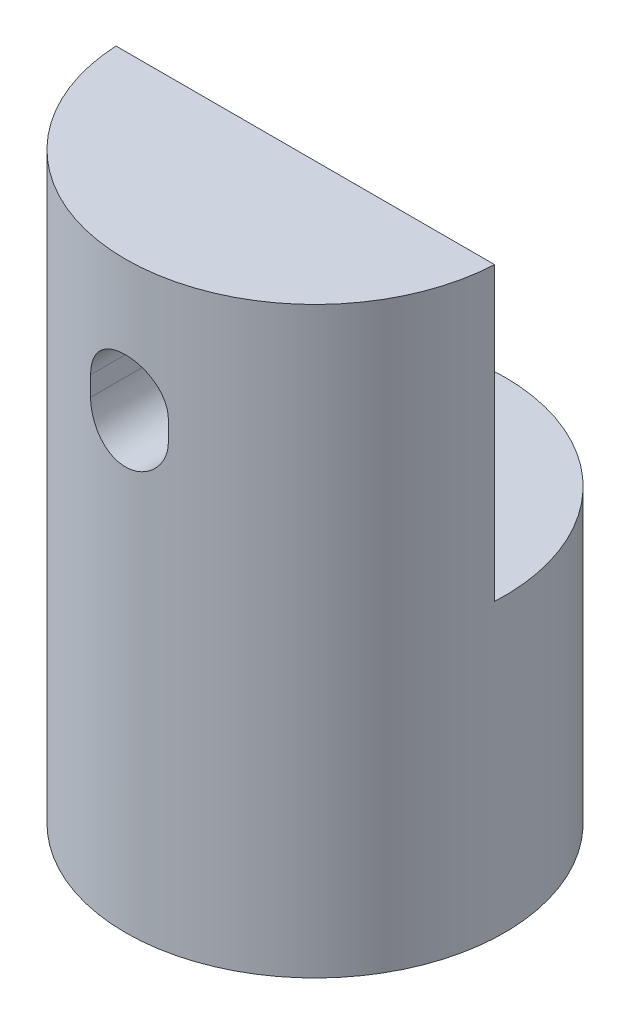
SolidWorks part; units mm, degrees
material "20% infill ABS"
ref_plane "Front" through (0, 0, 0) normal (0, 0, 1) x (1, 0, 0)
ref_plane "Top" through (0, 0, 0) normal (0, 1, 0) x (1, 0, 0)
ref_plane "Right" through (0, 0, 0) normal (1, 0, 0) x (0, 0, -1)
sketch "Sketch1" plane through (0, 0, 0) normal (0, 1, 0) x (1, 0, 0)
  circle A0 centre (0, 0) radius 9.75
  dimension "D1" = 19.5
extrude "Boss-Extrude1" add sketch "Sketch1" along normal blind 30
ref_plane "Plane1" through (9.75, 0, 0) normal (1, 0, 0) x (0, 0, -1)
sketch "Sketch3" plane through (0, 0, 0) normal (0, 0, 1) x (1, 0, 0)
  line L0 (9.75, -10.725) -> (9.75, 10.725) construction
  line L1 (-9.75, 30) -> (9.75, 30)
  line L2 (-9.75, 30) -> (-9.75, 15)
  line L3 (-9.75, 15) -> (9.75, 15)
  line L4 (9.75, 30) -> (9.75, 15)
  dimension "D1" = 15
extrude "Cut-Extrude1" cut sketch "Sketch3" against normal blind 30 and the other way blind 0.5
sketch "Sketch4" plane through (0, 0, 0.5) normal (0, 0, -1) x (-1, 0, 0)
  line L0 (0, 23.7438) -> (0, 22.7438) construction
  line L1 (2, 23.7438) -> (2, 22.7438)
  line L2 (-2, 23.7438) -> (-2, 22.7438)
  arc A1 (2, 23.7438) -> (-2, 23.7438) centre (0, 23.7438) ccw
  arc A2 (-2, 22.7438) -> (2, 22.7438) centre (0, 22.7438) ccw
  point P2 (0, 23.2438)
  point P8 (2, 23.2438)
  point P9 (0, 25.7438)
  point P10 (0, 20.7438)
  dimension "D1" = 4
  dimension "D2" = 5
extrude "Cut-Extrude2" cut sketch "Sketch4" against normal blind 30
